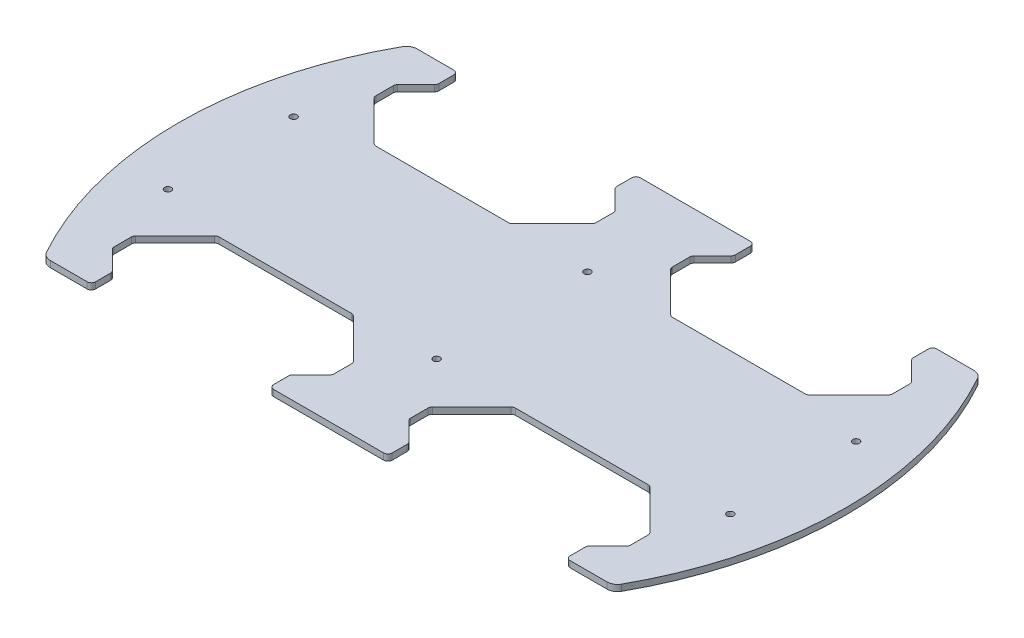
SolidWorks part; units mm, degrees
material "Acrylic (Medium-high impact)"
ref_plane "Front Plane" through (0, 0, 0) normal (0, 0, 1) x (1, 0, 0)
ref_plane "Top Plane" through (0, 0, 0) normal (0, 1, 0) x (1, 0, 0)
ref_plane "Right Plane" through (0, 0, 0) normal (1, 0, 0) x (0, 0, -1)
sketch "Sketch1" plane through (0, 0, 0) normal (0, 1, 0) x (1, 0, 0)
  line L1 (-150, -87.5) -> (150, -87.5) construction
  line L2 (-150, -87.5) -> (-150, 87.5) construction
  line L3 (-150, 87.5) -> (150, 87.5) construction
  line L4 (150, -87.5) -> (150, 87.5) construction
  line L5 (-150, -87.5) -> (150, 87.5) construction
  line L6 (-150, 87.5) -> (150, -87.5) construction
  line L7 (-94.037, 37.4826) -> (-29.037, 37.4826) construction
  line L12 (-150, 0) -> (150, 0) construction
  line L13 (-126.5544, 87.5) -> (-104.0544, 87.5)
  line L19 (54.4, -27.9) -> (64.4, -24.9) construction
  line L24 (-94.037, -37.4826) -> (-29.037, -37.4826) construction
  line L26 (-61.537, 37.4826) -> (-61.537, -37.4826) construction
  line L45 (80, 47.5) -> (80, -47.5) construction
  line L47 (37.5, 87.5) -> (-19.0544, 87.5)
  line L57 (-104.0544, 87.5) -> (-104.0544, 77.5)
  line L58 (-104.0544, 77.5) -> (-114.0544, 67.5)
  line L59 (-114.0544, 67.5) -> (-114.0544, 57.5)
  line L62 (-19.0544, 87.5) -> (-19.0544, 77.5)
  line L63 (-19.0544, 77.5) -> (-9.0544, 67.5)
  line L64 (-9.0544, 67.5) -> (-9.0544, 57.4651)
  line L65 (-9.0544, 57.4651) -> (-29.037, 37.4826)
  line L66 (-114.0544, 57.5) -> (-94.037, 37.4826)
  line L67 (-126.5544, -87.5) -> (-104.0544, -87.5)
  line L68 (-104.0544, -87.5) -> (-104.0544, -77.5)
  line L69 (-104.0544, -77.5) -> (-114.0544, -67.5)
  line L70 (-114.0544, -67.5) -> (-114.0544, -57.5)
  line L71 (-114.0544, -57.5) -> (-94.037, -37.4826)
  line L74 (-9.0544, -57.4651) -> (-29.037, -37.4826)
  line L75 (-9.0544, -67.5) -> (-9.0544, -57.4651)
  line L76 (-19.0544, -77.5) -> (-9.0544, -67.5)
  line L77 (-19.0544, -87.5) -> (-19.0544, -77.5)
  line L78 (37.5, -87.5) -> (-19.0544, -87.5)
  line L79 (122.5, -87.5) -> (136.956, -87.5)
  line L80 (122.5, 87.5) -> (136.956, 87.5)
  line L83 (54.4, 24.9) -> (64.4, 27.9) construction
  line L84 (54.4, 27.9) -> (64.4, 24.9) construction
  line L85 (54.4, -24.9) -> (64.4, -27.9) construction
  line L90 (-29.037, -37.4826) -> (-56.537, -37.4826)
  line L95 (-66.537, -37.4826) -> (-56.537, -37.4826)
  line L96 (-66.537, 37.4826) -> (-56.537, 37.4826)
  line L97 (-94.037, -37.4826) -> (-66.537, -37.4826)
  line L101 (-29.037, 37.4826) -> (-56.537, 37.4826)
  line L105 (-94.037, 37.4826) -> (-66.537, 37.4826)
  line L106 (0, 134.3792) -> (0, -127.0262) construction
  line L107 (80, 147.0664) -> (80, -140.2755) construction
  line L108 (-61.537, 165.7588) -> (-61.537, -140.2755) construction
  line L109 (72.1576, -37.5) -> (87.8424, -37.5)
  line L110 (87.8424, -37.5) -> (112.5, -37.5)
  line L111 (112.5, -37.5) -> (132.5, -57.5)
  line L112 (132.5, -57.5) -> (132.5, -67.5)
  line L113 (132.5, -67.5) -> (122.5, -77.5)
  line L114 (122.5, -77.5) -> (122.5, -87.5)
  line L115 (37.5, -77.5) -> (37.5, -87.5)
  line L116 (27.5, -67.5) -> (37.5, -77.5)
  line L117 (27.5, -57.5) -> (27.5, -67.5)
  line L118 (47.5, -37.5) -> (27.5, -57.5)
  line L119 (72.1576, -37.5) -> (47.5, -37.5)
  line L120 (122.5, 77.5) -> (122.5, 87.5)
  line L121 (132.5, 67.5) -> (122.5, 77.5)
  line L122 (132.5, 57.5) -> (132.5, 67.5)
  line L123 (112.5, 37.5) -> (132.5, 57.5)
  line L124 (87.8424, 37.5) -> (112.5, 37.5)
  line L125 (72.1576, 37.5) -> (87.8424, 37.5)
  line L126 (72.1576, 37.5) -> (47.5, 37.5)
  line L127 (47.5, 37.5) -> (27.5, 57.5)
  line L128 (27.5, 57.5) -> (27.5, 67.5)
  line L129 (27.5, 67.5) -> (37.5, 77.5)
  line L130 (37.5, 77.5) -> (37.5, 87.5)
  line L131 (9.233, 150.0546) -> (9.233, -136.8098) construction
  line L132 (136.956, 87.5) -> (145.0204, 87.5)
  line L133 (136.956, -87.5) -> (145.0204, -87.5)
  line L134 (4.233, 50.2735) -> (4.233, -32.8868) construction
  line L135 (150, 0) -> (168.466, 0) construction
  line L136 (-306.5379, 10) -> (-273.8396, 10) construction
  line L137 (-273.8396, 10) -> (-273.8396, -10) construction
  line L138 (-273.8396, -10) -> (-306.5379, -10) construction
  line L139 (-306.5379, -10) -> (-306.5379, -21) construction
  line L140 (-306.5379, -21) -> (-327.5379, 0) construction
  line L141 (-327.5379, 0) -> (-306.5379, 21) construction
  line L142 (-306.5379, 21) -> (-306.5379, 10) construction
  line L143 (150, 0) -> (168.466, 0) construction
  arc A7 (-126.5544, 87.5) -> (-126.5544, -87.5) centre (25, 0) ccw
  circle A11 centre (-125, -30) radius 1.6
  circle A12 centre (9.233, -36) radius 1.6
  circle A13 centre (143.46, -30) radius 1.6
  circle A14 centre (143.46, 30) radius 1.6
  circle A15 centre (9.233, 36) radius 1.6
  circle A16 centre (-125, 30) radius 1.6
  circle A17 centre (-15, 21) radius 1.6 construction
  circle A18 centre (9, 21) radius 1.6 construction
  circle A19 centre (9, -21) radius 1.6 construction
  circle A20 centre (-15, -21) radius 1.6 construction
  circle A21 centre (123.8, 13.4) radius 1.1 construction
  circle A22 centre (65, 13.4) radius 1.1 construction
  circle A23 centre (65, -13.4) radius 1.1 construction
  circle A24 centre (123.8, -13.4) radius 1.1 construction
  circle A27 centre (-61.537, -10) radius 1.6 construction
  circle A28 centre (-61.537, 10) radius 1.6 construction
  circle A29 centre (9.233, 0) radius 11 construction
  arc A30 (145.0204, 87.5) -> (145.0204, -87.5) centre (-6.534, 0) cw
  circle A31 centre (145, 0) radius 6.1 construction
  point P0 (0, 0)
  point P18 (59.4, 26.4)
  point P37 (59.4, -26.4)
  point P38 (0, 0)
  point P114 (80, -37.5)
  dimension "D15" = 12.2
  dimension "D19" = 3.2
  dimension "D21" = 3.2
  dimension "D23" = 125
  dimension "D24" = 175
  dimension "D26" = 3.2
  dimension "D28" = 85
  dimension "D34" = 145
  dimension "D22" = 3.2
  dimension "D16" = 3.2
  dimension "D38" = 3.2
  dimension "D40" = 2.2
  dimension "D47" = 42.5
  dimension "D45" = 22
  dimension "D1" = 175
  dimension "D2" = 300
  dimension "D4" = 10
  dimension "D5" = 135
  dimension "D6" = 135
  dimension "D7" = 80
  dimension "D8" = 70.77
  dimension "D9" = 22.5
  dimension "D10" = 5
  dimension "D11" = 10
  dimension "D12" = 10
  dimension "D13" = 3
  dimension "D14" = 20.6
  dimension "D17" = 135
  dimension "D18" = 65
  dimension "D20" = 10
  dimension "D25" = 10
  dimension "D27" = 143.46
  dimension "D29" = 10
  dimension "D30" = 135
  dimension "D31" = 10.0349
  dimension "D32" = 27.5
  dimension "D33" = 10
  dimension "D35" = 30
  dimension "D36" = 21
  dimension "D37" = 15
  dimension "D39" = 24
  dimension "D41" = 13.4
  dimension "D42" = 58.8
  dimension "D43" = 65
  dimension "D46" = 10
  dimension "D48" = 135
  dimension "D49" = 27.5
  dimension "D50" = 10
  dimension "D51" = 32.5
  dimension "D52" = 50
  dimension "D53" = 10
  dimension "D54" = 36
extrude "Boss-Extrude1" add sketch "Sketch1" along normal blind 3
fillet "Fillet1" radius 2 40 edges at (122.5, 1.5, -87.5) (122.5, 1.5, -77.5) (132.5, 1.5, -67.5) (132.5, 1.5, -57.5) (112.5, 1.5, -37.5) (47.5, 1.5, -37.5) (27.5, 1.5, -57.5) (27.5, 1.5, -67.5) (37.5, 1.5, -77.5) (37.5, 1.5, -87.5) (-19.0544, 1.5, -87.5) (-19.0544, 1.5, -77.5) (-9.0544, 1.5, -67.5) (-9.0544, 1.5, -57.4651) (-29.037, 1.5, -37.4826) (-94.037, 1.5, -37.4826) (-114.0544, 1.5, -57.5) (-114.0544, 1.5, -67.5) (-104.0544, 1.5, -77.5) (-104.0544, 1.5, -87.5) (122.5, 1.5, 87.5) (122.5, 1.5, 77.5) (132.5, 1.5, 67.5) (132.5, 1.5, 57.5) (112.5, 1.5, 37.5) (47.5, 1.5, 37.5) (27.5, 1.5, 57.5) (27.5, 1.5, 67.5) (37.5, 1.5, 77.5) (37.5, 1.5, 87.5) (-19.0544, 1.5, 87.5) (-19.0544, 1.5, 77.5) (-9.0544, 1.5, 67.5) (-9.0544, 1.5, 57.4651) (-29.037, 1.5, 37.4826) (-94.037, 1.5, 37.4826) (-114.0544, 1.5, 57.5) (-114.0544, 1.5, 67.5) (-104.0544, 1.5, 77.5) (-104.0544, 1.5, 87.5)
fillet "Fillet2" radius 5 4 edges at (-126.5544, 1.5, 87.5) (145.0204, 1.5, 87.5) (145.0204, 1.5, -87.5) (-126.5544, 1.5, -87.5)
